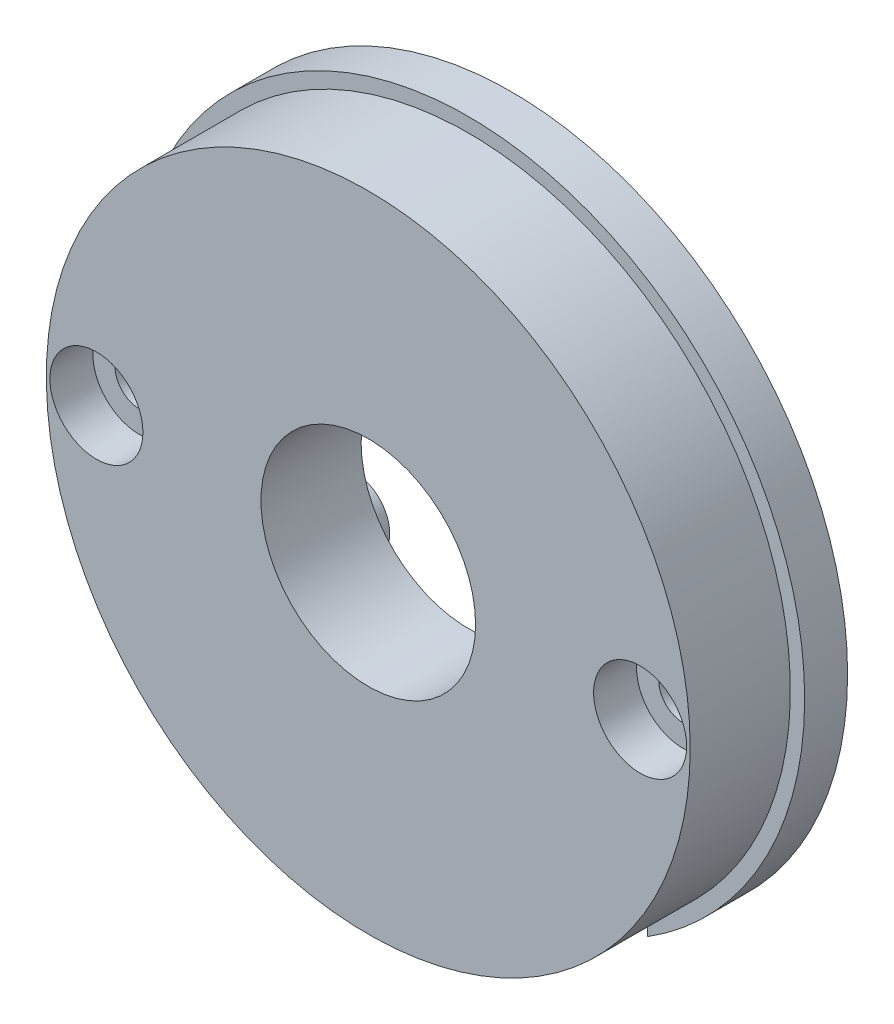
SolidWorks part; units mm, degrees
material "ABS"
ref_plane "正面" through (0, 0, 0) normal (0, 0, 1) x (1, 0, 0)
ref_plane "平面" through (0, 0, 0) normal (0, 1, 0) x (1, 0, 0)
ref_plane "右側面" through (0, 0, 0) normal (1, 0, 0) x (0, 0, -1)
sketch "ｽｹｯﾁ5" plane through (0, 0, 0) normal (0, 0, 1) x (1, 0, 0)
  circle A0 centre (0, 0) radius 22.5
  dimension "D1" = 45
extrude "ﾎﾞｽ - 押し出し2" add sketch "ｽｹｯﾁ5" along normal blind 10
sketch "ｽｹｯﾁ7" plane through (0, 0, 10) normal (0, 0, 1) x (1, 0, 0)
  line L1 (-19, 0) -> (0, -19) construction
  line L2 (-19, 0) -> (0, 19) construction
  line L3 (0, 19) -> (19, 0) construction
  line L4 (0, -19) -> (19, 0) construction
  line L5 (-19, 0) -> (19, 0) construction
  line L6 (0, 19) -> (0, -19) construction
  circle A0 centre (0, 0) radius 19 construction
  dimension "D1" = 38
sketch "ｽｹｯﾁ11" plane through (0, 0, 0) normal (0, 0, -1) x (-1, 0, 0)
  line L0 (0, 22.5) -> (0, -22.5) construction
  circle A0 centre (0, 0) radius 22.5 construction
hole_wizard "M3 穴付きねじ用座ぐり穴1" positions "ｽｹｯﾁ8" profile "ｽｹｯﾁ9" counterbore size "M3" standard "JIS" end condition through all
sketch "ｽｹｯﾁ8" plane through (0, 0, 10) normal (0, 0, 1) x (1, 0, 0)
  point P3 (19, 0)
  point P6 (-19, 0)
sketch "ｽｹｯﾁ9" plane through (19, 0, 10) normal (1, 0, 0) x (0, -1, 0)
  line L0 (0, 0) -> (0, 10)
  line L1 (0, 10) -> (1.7, 10)
  line L3 (1.7, 10) -> (1.7, 3)
  line L4 (1.7, 3) -> (3.25, 3)
  line L5 (3.25, 3) -> (3.25, 0)
  line L7 (3.25, 0) -> (0, 0)
  line L11 (0, -6.35) -> (0, 107.95) construction
  dimension "通し穴の直径" = 3.4
  dimension "通し穴の深さ" = 10
  dimension "座ぐり穴の直径" = 6.5
  dimension "座ぐり穴の深さ" = 3
sketch "ｽｹｯﾁ12" plane through (0, 0, 0) normal (0, 0, -1) x (-1, 0, 0)
  line L0 (0, 22.5) -> (0, -22.5) construction
  line L1 (-12.5, 17.5) -> (12.5, 17.5)
  line L2 (-12.5, 17.5) -> (-12.5, -22.5)
  line L3 (-12.5, -22.5) -> (12.5, -22.5)
  line L4 (12.5, 17.5) -> (12.5, -22.5)
  line L5 (-12.5, 17.5) -> (12.5, -22.5) construction
  line L6 (-12.5, -22.5) -> (12.5, 17.5) construction
  circle A0 centre (0, 0) radius 22.5 construction
  point P0 (0, -2.5)
  dimension "D1" = 25
  dimension "D2" = 40
extrude "ｶｯﾄ - 押し出し1" cut sketch "ｽｹｯﾁ12" against normal blind 3
sketch "ｽｹｯﾁ13" plane through (0, 0, 3) normal (0, 0, -1) x (-1, 0, 0)
  line L0 (-12.5, 3) -> (-9, 3)
  line L1 (-9, 5.5) -> (9, 5.5) construction
  line L2 (-9, 5.5) -> (-9, -5.5) construction
  line L3 (-9, -5.5) -> (9, -5.5) construction
  line L4 (9, 5.5) -> (9, -5.5) construction
  line L5 (-9, 5.5) -> (9, -5.5) construction
  line L6 (-9, -5.5) -> (9, 5.5) construction
  line L7 (-12.5, 17.5) -> (-12.5, -18.7083) construction
  line L8 (-12.5, 8) -> (-9, 8)
  line L9 (-12.5, 8) -> (-12.5, 3)
  arc A0 (-9, 3) -> (-9, 8) centre (-9, 5.5) ccw
  point P0 (0, 0)
  dimension "D3" = 2.5
  dimension "D1" = 11
  dimension "D2" = 18
extrude "ﾎﾞｽ - 押し出し3" add sketch "ｽｹｯﾁ13" along normal blind 1
sketch "ｽｹｯﾁ14" plane through (0, 0, 2) normal (0, 0, -1) x (-1, 0, 0)
  circle A0 centre (-9, 5.5) radius 1.75
  dimension "D1" = 3.5
extrude "ｶｯﾄ - 押し出し2" cut sketch "ｽｹｯﾁ14" against normal blind 3
mirror "ﾐﾗｰ1" about plane through (0, 0, 0) normal (1, 0, 0) of "ｶｯﾄ - 押し出し2", "ﾎﾞｽ - 押し出し3"
mirror "ﾐﾗｰ2" about plane through (0, 0, 0) normal (0, 1, 0) of "ﾐﾗｰ1", "ﾎﾞｽ - 押し出し3", "ｶｯﾄ - 押し出し2"
sketch "ｽｹｯﾁ16" plane through (0, 0, 10) normal (0, 0, 1) x (1, 0, 0)
  circle A0 centre (0, 0) radius 7.5
  dimension "D1" = 15
extrude "ｶｯﾄ - 押し出し3" cut sketch "ｽｹｯﾁ16" against normal through all
sketch "ｽｹｯﾁ17" plane through (0, 0, 0) normal (0, 0, -1) x (-1, 0, 0)
  line L0 (12.5, -18.7083) -> (12.5, -19.8997)
  line L1 (-12.5, -18.7083) -> (-12.5, -19.8997)
  line L2 (-12.5, 17.5) -> (-12.5, -18.7083) construction
  circle A0 centre (0, 0) radius 22.5
  circle A1 centre (0, 0) radius 23.5
  arc A2 (12.5, -18.7083) -> (-12.5, -18.7083) centre (0, 0) ccw construction
  arc M7 (12.5, -18.7083) -> (-12.5, -18.7083) centre (0, 0) ccw
  dimension "D1" = 1
extrude "ﾎﾞｽ - 押し出し4" add sketch "ｽｹｯﾁ17" against normal blind 3 contours L0 A1 L1 M7
